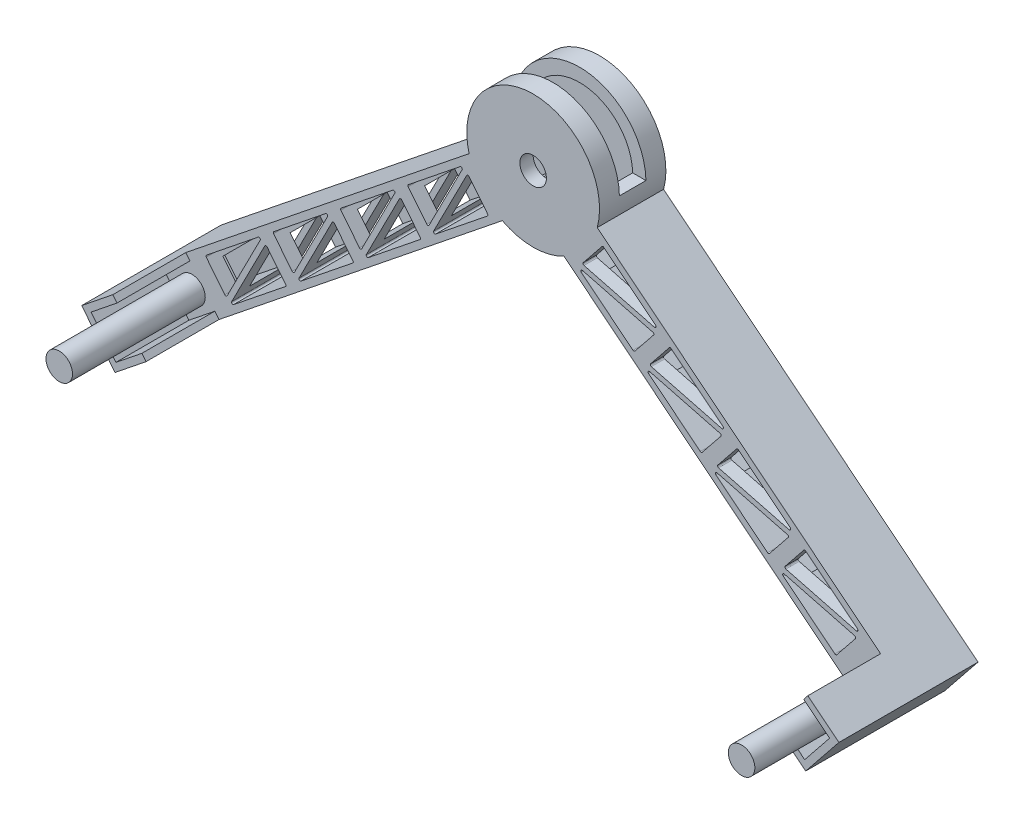
SolidWorks part; units mm, degrees
other "Markup1"
sketch "Sketch10" plane through (-187.1162, -34.3281, 104.7573) normal (-0.0779, -0.0282, 0.9966) x (0.967, 0.2412, 0.0824)
other "Markup2"
sketch "Sketch11" plane through (-187.1162, -34.3281, 104.7573) normal (-0.0779, -0.0282, 0.9966) x (0.967, 0.2412, 0.0824)
material "1060 Alloy"
ref_plane "Front Plane" through (0, 0, 0) normal (0, 0, 1) x (1, 0, 0)
ref_plane "Top Plane" through (0, 0, 0) normal (0, 1, 0) x (1, 0, 0)
ref_plane "Right Plane" through (0, 0, 0) normal (1, 0, 0) x (0, 0, -1)
sketch "Sketch1" plane through (0, 0, 0) normal (0, 0, 1) x (1, 0, 0)
  line L0 (-187.1162, 0) -> (375.3401, 0) construction
  line L1 (-187.1162, 0) -> (45.8528, 186.9213)
  line L2 (142.3711, 186.9213) -> (375.3401, 0)
  line L3 (-187.1162, 0) -> (-162.0839, -31.199)
  line L4 (-162.0839, -31.199) -> (70.8851, 155.7223)
  line L5 (117.3388, 155.7223) -> (350.3077, -31.199)
  line L6 (350.3077, -31.199) -> (375.3401, 0)
  arc A0 (70.8851, 155.7223) -> (117.3388, 155.7223) centre (94.1119, 200) ccw
  arc A1 (142.3711, 186.9213) -> (45.8528, 186.9213) centre (94.1119, 200) ccw
  dimension "D4" = 100
  dimension "D1" = 200
  dimension "D3" = 40
extrude "Boss-Extrude1" add sketch "Sketch1" along normal blind 50
shell "Shell1" thickness 10
sketch "Sketch2" plane through (0, 0, 50) normal (0, 0, 1) x (1, 0, 0)
  circle A0 centre (94.1119, 200) radius 10
  dimension "D1" = 20
extrude "Cut-Extrude1" cut sketch "Sketch2" against normal blind 50
ref_plane "Plane1" through (0, 251, 0) normal (0, 1, 0) x (1, 0, 0)
sketch "Sketch5" plane through (0, 251, 0) normal (0, 1, 0) x (1, 0, 0)
  line L0 (44.1119, 0) -> (44.1119, -50) construction
  line L1 (44.1119, -15) -> (144.1119, -15)
  line L2 (44.1119, -15) -> (44.1119, -35)
  line L3 (44.1119, -35) -> (144.1119, -35)
  line L4 (144.1119, -15) -> (144.1119, -35)
  line L5 (144.1119, -50) -> (144.1119, 0) construction
  line L6 (144.1119, 0) -> (44.1119, 0) construction
  dimension "D1" = 20
  dimension "D2" = 15
extrude "Cut-Extrude2" cut sketch "Sketch5" against normal blind 50
sketch "Sketch6" plane through (228.3429, -183.2096, 0) normal (0.78, -0.6258, 0) x (0, 0, -1)
  line L0 (-50, 234.8913) -> (0, 234.8913) construction
  line L1 (-40, 224.8913) -> (-10, 224.8913)
  line L2 (-40, 224.8913) -> (-40, 204.8913)
  line L3 (-40, 204.8913) -> (-10, 204.8913)
  line L4 (-10, 224.8913) -> (-10, 204.8913)
  line L5 (-50, 194.8913) -> (0, 194.8913) construction
  line L6 (0, 194.8913) -> (0, 234.8913) construction
  line L7 (-50, 194.8913) -> (-50, 234.8913) construction
  dimension "D1" = 10
  dimension "D2" = 10
  dimension "D3" = 10
  dimension "D4" = 10
extrude "Cut-Extrude3" cut sketch "Sketch6" against normal blind 50
sketch "Sketch7" plane through (228.3429, -183.2096, 0) normal (0.78, -0.6258, 0) x (0, 0, -1)
  line L0 (-50, 194.8913) -> (0, 194.8913) construction
  line L1 (0, 234.8913) -> (-4.7573, 234.8913)
  line L2 (0, 234.8913) -> (0, 194.8913)
  line L3 (0, 194.8913) -> (-4.7573, 194.8913)
  line L4 (-4.7573, 234.8913) -> (-4.7573, 194.8913)
extrude "Boss-Extrude2" add sketch "Sketch7" along normal blind 5
sketch "Sketch8" plane through (0, 0, 4.7573) normal (0, 0, 1) x (1, 0, 0)
  line L4 (375.3401, 0) -> (350.3077, -31.199)
  line L5 (350.3077, -31.199) -> (354.2076, -34.3281)
  line L6 (354.2076, -34.3281) -> (379.24, -3.129)
  line L7 (379.24, -3.129) -> (375.3401, 0)
  line L8 (375.3401, 0) -> (350.3077, -31.199)
  line L9 (350.3077, -31.199) -> (354.2076, -34.3281)
  line L10 (354.2076, -34.3281) -> (379.24, -3.129)
  line L11 (379.24, -3.129) -> (375.3401, 0)
  dimension "D1" = 0
extrude "Boss-Extrude3" add sketch "Sketch8" along normal blind 100
sketch "Sketch9" plane through (0, 0, 50) normal (0, 0, 1) x (1, 0, 0)
  line L0 (375.3401, 0) -> (355.8407, 15.6452)
  line L1 (375.3401, 0) -> (142.3711, 186.9213) construction
  line L2 (355.8407, 15.6452) -> (352.7117, 11.7454)
  line L3 (352.7117, 11.7454) -> (372.2111, -3.8999)
  line L4 (375.3401, 0) -> (350.3077, -31.199) construction
  line L5 (372.2111, -3.8999) -> (375.3401, 0)
  line L6 (350.3077, -31.199) -> (330.8083, -15.5538)
  line L7 (117.3388, 155.7223) -> (350.3077, -31.199) construction
  line L8 (330.8083, -15.5538) -> (333.9374, -11.6539)
  line L9 (333.9374, -11.6539) -> (353.4368, -27.2992)
  line L10 (350.3077, -31.199) -> (375.3401, 0) construction
  line L11 (353.4368, -27.2992) -> (350.3077, -31.199)
  dimension "D1" = 5
  dimension "D2" = 25
extrude "Boss-Extrude4" add sketch "Sketch9" along normal up to surface (54.7573 mm away) up to face at (364.7739, -17.164, 104.7573)
sketch "Sketch12" plane through (-113.8345, -91.3345, 0) normal (-0.78, -0.6258, 0) x (0, 0, 1)
  line L0 (50, 77.0991) -> (0, 77.0991) construction
  line L1 (0, 117.0991) -> (9.973, 117.0991)
  line L2 (0, 117.0991) -> (0, 77.0991)
  line L3 (0, 77.0991) -> (9.973, 77.0991)
  line L4 (9.973, 117.0991) -> (9.973, 77.0991)
extrude "Boss-Extrude5" add sketch "Sketch12" along normal blind 5
sketch "Sketch13" plane through (0, 0, 9.973) normal (0, 0, 1) x (1, 0, 0)
  line L4 (-162.0839, -31.199) -> (-187.1162, 0)
  line L5 (-187.1162, 0) -> (-191.0161, -3.129)
  line L6 (-191.0161, -3.129) -> (-165.9837, -34.3281)
  line L7 (-165.9837, -34.3281) -> (-162.0839, -31.199)
  line L8 (-162.0839, -31.199) -> (-187.1162, 0)
  line L9 (-187.1162, 0) -> (-191.0161, -3.129)
  line L10 (-191.0161, -3.129) -> (-165.9837, -34.3281)
  line L11 (-165.9837, -34.3281) -> (-162.0839, -31.199)
  dimension "D1" = 0
extrude "Boss-Extrude6" add sketch "Sketch13" along normal blind 95
sketch "Sketch14" plane through (0, 0, 50) normal (0, 0, 1) x (1, 0, 0)
  line L0 (-187.1162, 0) -> (-167.6168, 15.6452)
  line L1 (45.8528, 186.9213) -> (-187.1162, 0) construction
  line L2 (-167.6168, 15.6452) -> (-164.4878, 11.7454)
  line L3 (-164.4878, 11.7454) -> (-183.9872, -3.8999)
  line L4 (-187.1162, 0) -> (-162.0839, -31.199) construction
  line L5 (-183.9872, -3.8999) -> (-187.1162, 0)
  line L6 (-162.0839, -31.199) -> (-165.2129, -27.2992)
  line L7 (-165.2129, -27.2992) -> (-145.7135, -11.6539)
  line L8 (-145.7135, -11.6539) -> (-142.5845, -15.5538)
  line L9 (-162.0839, -31.199) -> (70.8851, 155.7223) construction
  line L10 (-142.5845, -15.5538) -> (-162.0839, -31.199)
  dimension "D1" = 5
  dimension "D2" = 25
extrude "Boss-Extrude7" add sketch "Sketch14" along normal up to surface (54.973 mm away) up to face at (-176.55, -17.164, 104.973)
sketch "Sketch15" plane through (0, 0, 50) normal (0, 0, 1) x (1, 0, 0)
  line L0 (-152.1623, 20.3525) -> (-138.11, 2.8384)
  line L1 (-136.4396, 3.0091) -> (-111.4931, 51.8137)
  line L2 (-113.0094, 53.0488) -> (-152.0082, 21.7583)
  line L3 (-106.341, 50.0074) -> (-92.2886, 32.4933)
  line L4 (-92.4428, 31.0875) -> (-131.4416, -0.2029)
  line L5 (-132.9578, 1.0322) -> (-108.0114, 49.8368)
  line L6 (45.8528, 186.9213) -> (-167.6168, 15.6452) construction
  line L7 (-142.5845, -15.5538) -> (70.8851, 155.7223) construction
  line L8 (-183.9872, -3.8999) -> (-165.2129, -27.2992) construction
  line L9 (-62.3109, 93.7264) -> (-101.3097, 62.4359)
  line L10 (-101.4639, 61.0301) -> (-87.4115, 43.516)
  line L11 (-85.7411, 43.6867) -> (-60.7947, 92.4913)
  line L12 (-82.2594, 41.7098) -> (-57.3129, 90.5144)
  line L13 (-55.6425, 90.6851) -> (-41.5902, 73.1709)
  line L14 (-41.7443, 71.7651) -> (-80.7431, 40.4747)
  line L15 (-11.6125, 134.404) -> (-50.6113, 103.1135)
  line L16 (-50.7654, 101.7077) -> (-36.7131, 84.1936)
  line L17 (-35.0427, 84.3643) -> (-10.0962, 133.1689)
  line L18 (-31.5609, 82.3874) -> (-6.6145, 131.192)
  line L19 (-4.9441, 131.3627) -> (9.1083, 113.8485)
  line L20 (8.9541, 112.4428) -> (-30.0447, 81.1523)
  line L21 (39.086, 175.0816) -> (0.0872, 143.7911)
  line L22 (-0.067, 142.3853) -> (13.9854, 124.8712)
  line L23 (15.6558, 125.0419) -> (40.6022, 173.8465)
  line L24 (19.1375, 123.065) -> (44.084, 171.8696)
  line L25 (45.7544, 172.0403) -> (59.8067, 154.5261)
  line L26 (59.6526, 153.1204) -> (20.6538, 121.8299)
  line L27 (322.8636, -1.4868) -> (336.9159, 16.0273)
  line L28 (336.3873, 17.621) -> (283.3361, 31.3974)
  line L29 (282.459, 29.6495) -> (321.4578, -1.641)
  line L30 (338.4397, 23.1964) -> (299.4409, 54.4868)
  line L31 (298.0352, 54.3327) -> (283.9828, 36.8185)
  line L32 (284.5114, 35.2248) -> (337.5626, 21.4485)
  line L33 (117.3388, 155.7223) -> (330.8083, -15.5538) construction
  line L34 (355.8407, 15.6452) -> (142.3711, 186.9213) construction
  line L35 (353.4368, -27.2992) -> (372.2111, -3.8999) construction
  line L36 (233.8146, 75.9011) -> (286.8658, 62.1248)
  line L37 (287.7429, 63.8727) -> (248.7441, 95.1631)
  line L38 (247.3383, 95.009) -> (233.286, 77.4948)
  line L39 (231.7622, 70.3258) -> (270.761, 39.0353)
  line L40 (272.1667, 39.1895) -> (286.2191, 56.7036)
  line L41 (285.6905, 58.2973) -> (232.6393, 72.0737)
  line L42 (183.1178, 116.5774) -> (236.169, 102.8011)
  line L43 (237.0461, 104.5489) -> (198.0473, 135.8394)
  line L44 (196.6415, 135.6852) -> (182.5892, 118.1711)
  line L45 (181.0653, 111.0021) -> (220.0641, 79.7116)
  line L46 (221.4699, 79.8658) -> (235.5223, 97.3799)
  line L47 (234.9937, 98.9736) -> (181.9425, 112.75)
  line L48 (132.421, 157.2537) -> (185.4721, 143.4774)
  line L49 (186.3493, 145.2252) -> (147.3505, 176.5157)
  line L50 (145.9447, 176.3615) -> (131.8924, 158.8474)
  line L51 (130.3685, 151.6784) -> (169.3673, 120.3879)
  line L52 (170.7731, 120.5421) -> (184.8255, 138.0562)
  line L53 (184.2968, 139.6499) -> (131.2457, 153.4263)
  arc A0 (-152.1623, 20.3525) -> (-152.0082, 21.7583) centre (-151.3824, 20.9783) cw
  arc A1 (-136.4396, 3.0091) -> (-138.11, 2.8384) centre (-137.33, 3.4642) cw
  arc A2 (-111.4931, 51.8137) -> (-113.0094, 53.0488) centre (-112.3835, 52.2688) ccw
  arc A3 (-131.4416, -0.2029) -> (-132.9578, 1.0322) centre (-132.0674, 0.577) cw
  arc A4 (-92.4428, 31.0875) -> (-92.2886, 32.4933) centre (-93.0686, 31.8675) ccw
  arc A5 (-106.341, 50.0074) -> (-108.0114, 49.8368) centre (-107.1209, 49.3816) ccw
  arc A6 (-60.7947, 92.4913) -> (-62.3109, 93.7264) centre (-61.6851, 92.9464) ccw
  arc A7 (-101.4639, 61.0301) -> (-101.3097, 62.4359) centre (-100.6839, 61.6559) cw
  arc A8 (-85.7411, 43.6867) -> (-87.4115, 43.516) centre (-86.6316, 44.1418) cw
  arc A9 (-55.6425, 90.6851) -> (-57.3129, 90.5144) centre (-56.4225, 90.0592) ccw
  arc A10 (-80.7431, 40.4747) -> (-82.2594, 41.7098) centre (-81.3689, 41.2547) cw
  arc A11 (-41.7443, 71.7651) -> (-41.5902, 73.1709) centre (-42.3701, 72.5451) ccw
  arc A12 (-10.0962, 133.1689) -> (-11.6125, 134.404) centre (-10.9867, 133.624) ccw
  arc A13 (-50.7654, 101.7077) -> (-50.6113, 103.1135) centre (-49.9855, 102.3335) cw
  arc A14 (-35.0427, 84.3643) -> (-36.7131, 84.1936) centre (-35.9331, 84.8194) cw
  arc A15 (-4.9441, 131.3627) -> (-6.6145, 131.192) centre (-5.724, 130.7369) ccw
  arc A16 (-30.0447, 81.1523) -> (-31.5609, 82.3874) centre (-30.6705, 81.9323) cw
  arc A17 (8.9541, 112.4428) -> (9.1083, 113.8485) centre (8.3283, 113.2227) ccw
  arc A18 (40.6022, 173.8465) -> (39.086, 175.0816) centre (39.7118, 174.3016) ccw
  arc A19 (-0.067, 142.3853) -> (0.0872, 143.7911) centre (0.713, 143.0111) cw
  arc A20 (15.6558, 125.0419) -> (13.9854, 124.8712) centre (14.7653, 125.497) cw
  arc A21 (45.7544, 172.0403) -> (44.084, 171.8696) centre (44.9744, 171.4145) ccw
  arc A22 (20.6538, 121.8299) -> (19.1375, 123.065) centre (20.028, 122.6099) cw
  arc A23 (59.6526, 153.1204) -> (59.8067, 154.5261) centre (59.0268, 153.9003) ccw
  arc A24 (336.9159, 16.0273) -> (336.3873, 17.621) centre (336.1359, 16.6531) ccw
  arc A25 (322.8636, -1.4868) -> (321.4578, -1.641) centre (322.0836, -0.861) cw
  arc A26 (282.459, 29.6495) -> (283.3361, 31.3974) centre (283.0848, 30.4295) cw
  arc A27 (337.5626, 21.4485) -> (338.4397, 23.1964) centre (337.8139, 22.4164) ccw
  arc A28 (284.5114, 35.2248) -> (283.9828, 36.8185) centre (284.7628, 36.1927) cw
  arc A29 (299.4409, 54.4868) -> (298.0352, 54.3327) centre (298.8151, 53.7068) ccw
  arc A30 (233.8146, 75.9011) -> (233.286, 77.4948) centre (234.066, 76.869) cw
  arc A31 (286.8658, 62.1248) -> (287.7429, 63.8727) centre (287.1171, 63.0927) ccw
  arc A32 (248.7441, 95.1631) -> (247.3383, 95.009) centre (248.1183, 94.3831) ccw
  arc A33 (231.7622, 70.3258) -> (232.6393, 72.0737) centre (232.388, 71.1058) cw
  arc A34 (272.1667, 39.1895) -> (270.761, 39.0353) centre (271.3868, 39.8153) cw
  arc A35 (286.2191, 56.7036) -> (285.6905, 58.2973) centre (285.4391, 57.3294) ccw
  arc A36 (183.1178, 116.5774) -> (182.5892, 118.1711) centre (183.3691, 117.5453) cw
  arc A37 (236.169, 102.8011) -> (237.0461, 104.5489) centre (236.4203, 103.769) ccw
  arc A38 (198.0473, 135.8394) -> (196.6415, 135.6852) centre (197.4215, 135.0594) ccw
  arc A39 (181.0653, 111.0021) -> (181.9425, 112.75) centre (181.6912, 111.7821) cw
  arc A40 (221.4699, 79.8658) -> (220.0641, 79.7116) centre (220.69, 80.4916) cw
  arc A41 (235.5223, 97.3799) -> (234.9937, 98.9736) centre (234.7423, 98.0057) ccw
  arc A42 (132.421, 157.2537) -> (131.8924, 158.8474) centre (132.6723, 158.2216) cw
  arc A43 (185.4721, 143.4774) -> (186.3493, 145.2252) centre (185.7235, 144.4453) ccw
  arc A44 (147.3505, 176.5157) -> (145.9447, 176.3615) centre (146.7247, 175.7357) ccw
  arc A45 (130.3685, 151.6784) -> (131.2457, 153.4263) centre (130.9943, 152.4584) cw
  arc A46 (170.7731, 120.5421) -> (169.3673, 120.3879) centre (169.9931, 121.1679) cw
  arc A47 (184.8255, 138.0562) -> (184.2968, 139.6499) centre (184.0455, 138.682) ccw
  point P12 (-152.7881, 21.1325)
  point P15 (-137.1429, 1.6331)
  point P22 (-91.6628, 31.7133)
  point P25 (-107.308, 51.2128)
  point P97 (337.883, 17.2326)
  point P100 (322.2378, -2.2668)
  point P103 (278.8183, 32.5705)
  dimension "D5" = 1
  dimension "D6" = 1
  dimension "D17" = 1
  dimension "D1" = 5
  dimension "D2" = 5
  dimension "D3" = 25
  dimension "D4" = 25
  dimension "D7" = 50
  dimension "D8" = 4
  dimension "D9" = 40
  dimension "D11" = 25
  dimension "D12" = 50
  dimension "D13" = 5
  dimension "D14" = 4
  dimension "D15" = 5
  dimension "D16" = 40
  dimension "D19" = 10.7
  dimension "D10" = 4
  dimension "D18" = 4
extrude "Cut-Extrude4" cut sketch "Sketch15" against normal blind 95
sketch "Sketch16" plane through (0, 0, 50) normal (0, 0, 1) x (1, 0, 0)
  line L2 (-183.9872, -3.8999) -> (-164.4878, 11.7454) construction
  line L4 (-183.9872, -3.8999) -> (-165.2129, -27.2992) construction
  circle A0 centre (-162.9004, -6.2124) radius 10
  dimension "D1" = 20
  dimension "D2" = 15
  dimension "D3" = 15
extrude "Boss-Extrude8" add sketch "Sketch16" along normal blind 100
sketch "Sketch18" plane through (0, 0, 50) normal (0, 0, 1) x (1, 0, 0)
  line L0 (353.4368, -27.2992) -> (333.9374, -11.6539) construction
  line L1 (372.2111, -3.8999) -> (353.4368, -27.2992) construction
  circle A0 centre (351.1243, -6.2124) radius 10
  dimension "D1" = 20
  dimension "D2" = 15
  dimension "D3" = 15
extrude "Boss-Extrude9" add sketch "Sketch18" along normal blind 100
